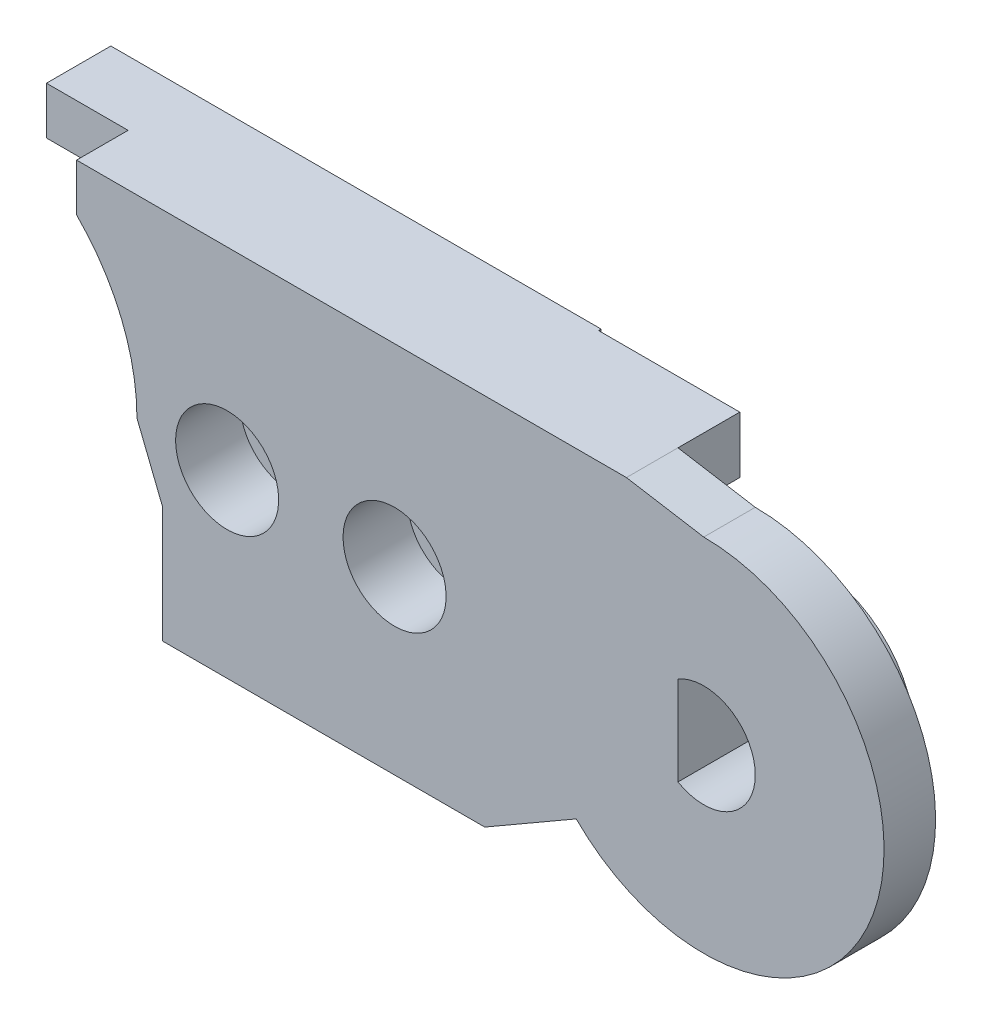
SolidWorks part; units mm, degrees
ref_plane "Front Plane" through (0, 0, 0) normal (0, 0, 1) x (1, 0, 0)
ref_plane "Top Plane" through (0, 0, 0) normal (0, 1, 0) x (1, 0, 0)
ref_plane "Right Plane" through (0, 0, 0) normal (1, 0, 0) x (0, 0, -1)
sketch "Sketch3" plane through (0, 0, 0) normal (0, 0, 1) x (1, 0, 0)
  line L7 (8, 0) -> (9, -2.5)
  line L11 (30, 7) -> (27, 7.5)
  line L13 (0, 7) -> (0, 7.5) construction
  line L14 (0, 7.5) -> (-22.3287, 7.5) construction
  line L15 (0, 5.3) -> (-14, 5.3) construction
  line L16 (0, 4) -> (-14, 4) construction
  line L17 (-14, 4) -> (-14, 5.3) construction
  line L18 (5.6569, 5.6569) -> (5.6569, 7.5)
  line L19 (5.6569, 7.5) -> (27, 7.5)
  line L20 (21.5, -7) -> (9, -7)
  line L21 (9, -7) -> (9, -2.5)
  line L23 (25.0503, -4.9497) -> (21.5, -7)
  arc A4 (8, 0) -> (5.6569, 5.6569) centre (0, 0) ccw
  arc A5 (25.0503, -4.9497) -> (30, 7) centre (30, 0) ccw
  circle A6 centre (0, 0) radius 7 construction
  circle A7 centre (0, 0) radius 3.9 construction
  circle A8 centre (0, 0) radius 5.3 construction
  circle A9 centre (0, 0) radius 4 construction
  dimension "D10" = 0.5
  dimension "D17" = 14
  dimension "D5" = 135
  dimension "D6" = 12.5
  dimension "D7" = 4.5
  dimension "D8" = 1
  dimension "D9" = 45
  dimension "D11" = 1.8431
  dimension "D12" = 30
  dimension "D14" = 3
extrude "Boss-Extrude1" add sketch "Sketch3" along normal blind 2 contours A5 L11 L19 L18 A4 L7 L21 L20 L23
sketch "Sketch20" plane through (0, 0, 0) normal (0, 0, 1) x (1, 0, 0)
  line L0 (0, 7) -> (0, 7.5) construction
  line L1 (0, 7.5) -> (-19.4737, 7.5) construction
  line L2 (0, 5.3) -> (-14, 5.3) construction
  line L3 (0, 4) -> (-14, 4) construction
  line L4 (-14, 4) -> (-14, 5.3) construction
  line L5 (0, 5.3) -> (17.4849, 5.3) construction
  line L6 (17.4849, 5.3) -> (17.4849, 4) construction
  line L7 (17.4849, 4) -> (0, 4) construction
  line L8 (-2.5, 7.5) -> (-2.5, 2.868) construction
  circle A0 centre (0, 0) radius 7 construction
  circle A1 centre (0, 0) radius 3.9 construction
  circle A3 centre (0, 0) radius 5.3 construction
  circle A4 centre (0, 0) radius 4 construction
  circle A5 centre (0, 0) radius 2 construction
  dimension "D1" = 0
  dimension "D2" = 2.5
ref_plane "Plane1" through (0, 0, 2) normal (0, 0, 1) x (1, 0, 0)
sketch "Sketch4" plane through (0, 0, 2) normal (0, 0, 1) x (1, 0, 0)
  line L4 (5.6569, 5.6569) -> (5.6569, 7.5)
  line L5 (5.6569, 5.6569) -> (5.6569, 7.5) construction
  line L6 (5.6569, 7.5) -> (21.5, 7.5)
  line L10 (8, 0) -> (9, -2.5)
  line L11 (9, -2.5) -> (9, -7)
  line L12 (9, -7) -> (21.5, -7)
  line L13 (21.5, -7) -> (21.5, 7.5)
  arc A0 (8, 0) -> (5.6569, 5.6569) centre (0, 0) ccw construction
  arc A3 (8, 0) -> (5.6569, 5.6569) centre (0, 0) ccw
sketch "Sketch22" plane through (0, 0, 2) normal (0, 0, 1) x (1, 0, 0)
  line L0 (5.6569, 5.6569) -> (2.4868, 5.6569)
  line L1 (5.6569, 7.5) -> (21.5, 7.5)
  line L2 (5.6569, 7.5) -> (2.4868, 7.5)
  line L3 (2.4868, 7.5) -> (2.4868, 5.6569)
  line L6 (8, 0) -> (9, -2.5)
  line L7 (9, -2.5) -> (9, -7)
  line L8 (9, -7) -> (21.5, -7)
  line L10 (21.5, 7.5) -> (27, 7.5)
  line L11 (27, 7.5) -> (27, 2.172)
  line L12 (27, 2.172) -> (23.2751, 2.172)
  line L13 (21.5, -7) -> (23.2751, -5.9749)
  line L14 (25.0503, -4.9497) -> (21.5, -7) construction
  line L15 (23.2751, -5.9749) -> (23.2751, 2.172)
  arc A0 (8, 0) -> (5.6569, 5.6569) centre (0, 0) ccw
extrude "Boss-Extrude6" add sketch "Sketch22" along normal blind 2.5
sketch "Sketch25" plane through (0, 0, 2) normal (0, 0, 1) x (1, 0, 0)
  line L0 (0, 5.3) -> (18.0981, 5.3) construction
  line L1 (0, 4) -> (18.0981, 4) construction
  line L2 (18.0981, 4) -> (18.0981, 5.3) construction
sketch "Sketch26" plane through (0, 0, 2) normal (0, 0, 1) x (1, 0, 0)
  line L1 (18.0981, 5.3) -> (2.5301, 5.3)
  line L2 (18.0981, 4) -> (2.5301, 4)
  line L3 (2.5301, 5.3) -> (2.5301, 4)
  line L4 (18.0981, 5.3) -> (27, 5.3)
  line L5 (27, 2.172) -> (27, 7.5) construction
  line L6 (27, 5.3) -> (27, 4)
  line L7 (27, 4) -> (18.0981, 4)
extrude "Cut-Extrude6" cut sketch "Sketch26" along normal blind 2.5
ref_plane "Plane18" through (0, 0, 4.5) normal (0, 0, 1) x (1, 0, 0)
sketch "Sketch31" plane through (0, 0, 4.5) normal (0, 0, 1) x (1, 0, 0)
  line L0 (2.4327, 5.6569) -> (0, 5.6569)
  line L4 (9, -5.6569) -> (0, -5.6569)
  line L5 (2.4327, 5.6569) -> (2.4868, 7.5)
  line L12 (9, -7) -> (9, -5.6569)
  line L13 (9, -2.5) -> (9, -7) construction
  line L16 (27, 7.5) -> (27, 2.172)
  line L17 (27, 2.172) -> (23.2751, 2.172)
  line L18 (23.2751, -5.9749) -> (23.2751, 2.172)
  line L19 (27, 7.5) -> (2.4868, 7.5)
  line L20 (9, -7) -> (21.5, -7)
  line L21 (21.5, -7) -> (23.2751, -5.9749)
  arc A0 (0, 5.6569) -> (0, -5.6569) centre (0, 0) ccw
  dimension "D1" = 5.6569
extrude "Boss-Extrude14" add sketch "Sketch31" along normal blind 2.3 separate body
sketch "Sketch32" plane through (0, 0, 6.8) normal (0, 0, 1) x (1, 0, 0)
  circle A0 centre (0, 0) radius 2.1
extrude "Cut-Extrude7" cut sketch "Sketch32" against normal blind 2.3
sketch "Sketch33" plane through (0, 0, 6.8) normal (0, 0, 1) x (1, 0, 0)
  line L4 (9, -5.6569) -> (9, -7)
  line L11 (9, -7) -> (21.5, -7)
  line L15 (21.5, -7) -> (21.5, -5.6569)
  line L16 (21.5, -5.6569) -> (9, -5.6569)
  line L17 (2.4868, 7.5) -> (21.5, 7.5)
  line L18 (27, 7.5) -> (2.4868, 7.5) construction
  line L19 (2.4868, 7.5) -> (2.4327, 5.6569)
  line L20 (2.4327, 5.6569) -> (21.5, 5.6569)
  line L21 (21.5, 5.6569) -> (21.5, 7.5)
extrude "Boss-Extrude15" add sketch "Sketch33" along normal blind 1.2
sketch "Sketch34" plane through (0, 0, 2) normal (0, 0, 1) x (1, 0, 0)
  line L0 (30, 5.3) -> (18.0981, 5.3) construction
  line L1 (30, 4) -> (18.0981, 4) construction
  circle A0 centre (30, 0) radius 2 construction
  circle A1 centre (30, 0) radius 5.3 construction
  circle A2 centre (30, 0) radius 4 construction
sketch "Sketch35" plane through (0, 0, 6.8) normal (0, 0, 1) x (1, 0, 0)
  line L0 (27, 2.172) -> (27, 7.5)
  line L1 (27, 2.172) -> (21.5204, 2.172)
  line L2 (27, 7.5) -> (21.5204, 7.5)
  line L3 (21.5204, 2.172) -> (21.5204, 7.5)
  line L4 (27, 2.172) -> (27, 7.5) construction
  line L5 (27, 7.5) -> (21.5, 7.5) construction
  dimension "D1" = 0
extrude "Cut-Extrude8" cut sketch "Sketch35" against normal blind 2.4
sketch "Sketch36" plane through (0, 0, 4.4) normal (0, 0, 1) x (1, 0, 0)
  line L0 (27, 2.172) -> (27, 4)
  line L1 (27, 2.172) -> (23.3, 2.172)
  line L2 (27, 4) -> (23.3, 4)
  line L3 (23.3, 2.172) -> (23.3, 4)
  line L4 (21.5, -7) -> (21.5, 7.5) construction
  dimension "D1" = 1.8
extrude "Cut-Extrude9" cut sketch "Sketch36" against normal blind 2.4
sketch "Sketch37" plane through (0, 0, 2) normal (0, 0, 1) x (1, 0, 0)
  circle A0 centre (30, 0) radius 3.9
extrude "Boss-Extrude16" add sketch "Sketch37" along normal blind 2.3
sketch "Sketch39" plane through (0, 0, 4.3) normal (0, 0, 1) x (1, 0, 0)
  line L0 (29, 1.7321) -> (29, -1.7321)
  arc A0 (29, -1.7321) -> (29, 1.7321) centre (30, 0) ccw
  dimension "D2" = 4
  dimension "D1" = 1
extrude "Cut-Extrude10" cut sketch "Sketch39" against normal through all
sketch "Sketch43" plane through (0, 0, 6.8) normal (0, 0, 1) x (1, 0, 0)
  line L2 (0, -5.6569) -> (9, -5.6569) construction
  circle A0 centre (11.5, 0) radius 2.5
  circle A1 centre (18, 0) radius 2.5
  dimension "D1" = 2.5
  dimension "D3" = 5
  dimension "D4" = 6.5
  dimension "D2" = 5.6569
extrude "Boss-Extrude17" add sketch "Sketch43" along normal blind 1.2
sketch "Sketch44" plane through (0, 0, 8) normal (0, 0, 1) x (1, 0, 0)
  circle A0 centre (11.5, 0) radius 0.95
  circle A1 centre (18, 0) radius 0.95
  dimension "D1" = 1.9
  dimension "D2" = 1.9
extrude "Cut-Extrude11" cut sketch "Sketch44" against normal through all
sketch "Sketch45" plane through (0, 0, 0) normal (0, 0, -1) x (-1, 0, 0)
  circle A0 centre (-11.5, 0) radius 2
  circle A1 centre (-18, 0) radius 2
extrude "Cut-Extrude12" cut sketch "Sketch45" against normal blind 2.5
ref_plane "Plane17" through (0, 0, 8) normal (0, 0, 1) x (1, 0, 0)
sketch "Sketch48" plane through (0, 0, 2) normal (0, 0, 1) x (1, 0, 0)
  circle A0 centre (30, 0) radius 5 construction
sketch "Sketch51" plane through (0, 0, 8) normal (0, 0, 1) x (1, 0, 0)
  line L0 (18.2355, 5.6569) -> (27.0112, -4.8677) construction
  line L1 (2.4327, 5.6569) -> (21.5, 5.6569) construction
sketch "Sketch52" plane through (0, 5.6569, 0) normal (0, -1, 0) x (1, 0, 0)
  circle A0 centre (18.2355, 8) radius 0.75
extrude "Cut-Extrude13" cut sketch "Sketch52" along direction (0.6404, -0.768, 0) on the side against the normal blind 10
split "Split1" trim tools "Plane18" bodies to split 133 129 resulting bodies 135 136
mirror "Mirror1" about plane through (0, 0, 8) normal (0, 0, 1) of bodies 135 136
delete or keep bodies "Body-Delete/Keep 1" type delete bodies bodies 135 136 137
